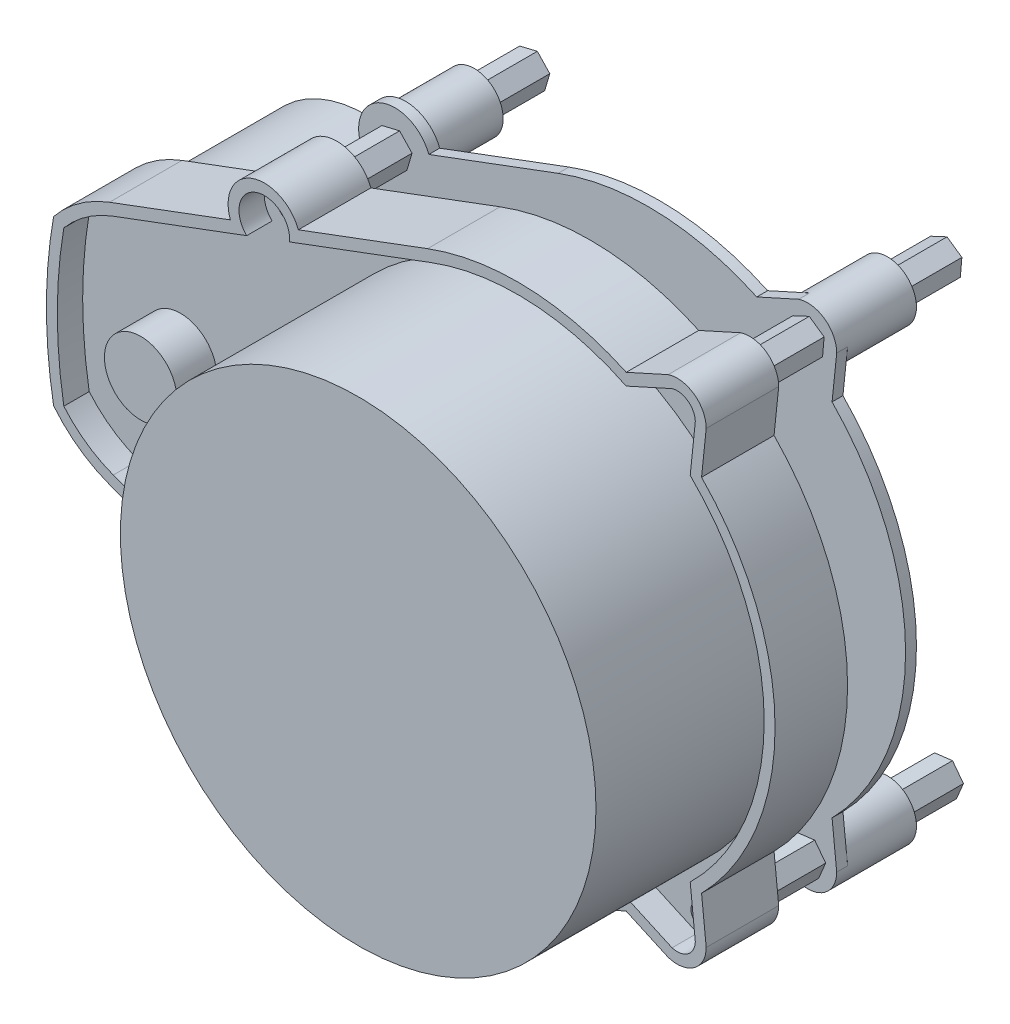
SolidWorks part; units mm, degrees
ref_plane "Plan de face" through (0, 0, 0) normal (0, 0, 1) x (1, 0, 0)
ref_plane "Plan de dessus" through (0, 0, 0) normal (0, 1, 0) x (1, 0, 0)
ref_plane "Plan de droite" through (0, 0, 0) normal (1, 0, 0) x (0, 0, -1)
sketch "Esquisse1" plane through (0, 0, 0) normal (0, 0, 1) x (1, 0, 0)
  line L0 (-12.425, 33.2546) -> (-30.2572, 26.5919)
  line L1 (-56.3, 16.8615) -> (-56.3, -16.8615) construction
  line L2 (-50, 0) -> (0, 0) construction
  line L3 (-12.425, 33.2546) -> (-12.425, -33.2546) construction
  line L5 (-35, 25) -> (-34.9409, 24.8419) construction
  line L6 (-39.6247, 23.0919) -> (-56.3, 16.8615)
  line L7 (-33.4505, 25.3988) -> (-36.4314, 24.2851)
  line L8 (20.756, 34.8016) -> (14.974, 32.1874)
  line L9 (26, 31) -> (25.36, 24.8419)
  line L10 (-65, 0) -> (35.5, 0) construction
  line L11 (55, 0) -> (-55, 0) construction
  line L12 (-35, -25) -> (-34.9409, -24.8419) construction
  line L13 (26, -31) -> (25.36, -24.8419)
  line L14 (20.756, -34.8016) -> (14.974, -32.1874)
  line L15 (-33.4505, -25.3988) -> (-36.4314, -24.2851)
  line L16 (-39.6247, -23.0919) -> (-56.3, -16.8615)
  line L17 (-12.425, -33.2546) -> (-30.2572, -26.5919)
  arc A1 (25.36, -24.8419) -> (25.36, 24.8419) centre (0, 0) ccw
  arc A3 (-64.01, 11.3013) -> (-64.01, -11.3013) centre (0, 0) ccw
  arc A4 (-56.3, 16.8615) -> (-64.01, 11.3013) centre (-50, 0) ccw
  circle A5 centre (22, 31) radius 1.6
  circle A6 centre (-35, 25) radius 1.6
  arc A7 (-30.2572, 26.5919) -> (-39.6247, 23.0919) centre (-34.9409, 24.8419) ccw
  arc A8 (26, 31) -> (20.756, 34.8016) centre (22, 31) ccw
  arc A9 (14.974, 32.1874) -> (-12.425, 33.2546) centre (0, 0) ccw
  arc A10 (14.974, -32.1874) -> (-12.425, -33.2546) centre (0, 0) cw
  arc A11 (26, -31) -> (20.756, -34.8016) centre (22, -31) cw
  arc A12 (-30.2572, -26.5919) -> (-39.6247, -23.0919) centre (-34.9409, -24.8419) cw
  circle A13 centre (-35, -25) radius 1.6
  circle A14 centre (22, -31) radius 1.6
  arc A15 (-56.3, -16.8615) -> (-64.01, -11.3013) centre (-50, 0) cw
  point P28 (-12.425, 0)
  point P29 (-56.3, 0)
  dimension "D1" = 71
  dimension "D4" = 130
  dimension "D6" = 3.2
  dimension "D10" = 10
  dimension "D11" = 8
  dimension "D3" = 50
  dimension "D5" = 31
  dimension "D7" = 22
  dimension "D8" = 35
  dimension "D9" = 25
extrude "Boss.-Extru.1" add sketch "Esquisse1" along normal blind 10 contours A15 L16 A12 L17 A10 L14 A11 L13 A1 L9 A8 L8 A9 L0 A7 L6 A4 A3 A13 A5 A6 A14
sketch "Esquisse2" plane through (0, 0, 10) normal (0, 0, 1) x (1, 0, 0)
  circle A0 centre (0, 0) radius 32.8
  dimension "D1" = 65.6
extrude "Boss.-Extru.2" add sketch "Esquisse2" along normal blind 22
sketch "Esquisse3" plane through (0, 0, 10) normal (0, 0, 1) x (1, 0, 0)
  line L16 (-55.775, -15.4564) -> (-37.3782, -22.33)
  line L17 (14.9568, -30.5335) -> (21.2911, -33.3974)
  line L18 (24.4991, -31.0687) -> (23.7942, -24.2866)
  line L19 (23.7942, 24.2866) -> (24.4991, 31.0687)
  line L20 (21.2911, 33.3974) -> (14.9568, 30.5335)
  line L21 (-11.9, 31.8495) -> (-31.4537, 24.5436)
  line L22 (-55.775, -15.4564) -> (-37.3782, -22.33)
  line L23 (14.9568, -30.5335) -> (21.2911, -33.3974)
  line L24 (24.4991, -31.0687) -> (23.7942, -24.2866)
  line L25 (23.7942, 24.2866) -> (24.4991, 31.0687)
  line L26 (21.2911, 33.3974) -> (14.9568, 30.5335)
  line L27 (-11.9, 31.8495) -> (-31.4537, 24.5436)
  line L28 (-31.4537, -24.5436) -> (-11.9, -31.8495)
  line L29 (-31.4537, -24.5436) -> (-11.9, -31.8495)
  line L30 (-37.3782, 22.33) -> (-55.775, 15.4564)
  line L31 (-37.3782, 22.33) -> (-55.775, 15.4564)
  arc A20 (-62.6, -10.6532) -> (-55.775, -15.4564) centre (-50, 0) ccw
  arc A21 (-11.9, -31.8495) -> (14.9568, -30.5335) centre (0, 0) ccw
  arc A22 (23.7942, -24.2866) -> (23.7942, 24.2866) centre (0, 0) ccw
  arc A23 (14.9568, 30.5335) -> (-11.9, 31.8495) centre (0, 0) ccw
  arc A24 (-55.775, 15.4564) -> (-62.6, 10.6532) centre (-50, 0) ccw
  arc A25 (-62.6, 10.6532) -> (-62.6, -10.6532) centre (0, 0) ccw
  arc A26 (-62.6, -10.6532) -> (-55.775, -15.4564) centre (-50, 0) ccw
  arc A27 (-11.9, -31.8495) -> (14.9568, -30.5335) centre (0, 0) ccw
  arc A28 (23.7942, -24.2866) -> (23.7942, 24.2866) centre (0, 0) ccw
  arc A29 (14.9568, 30.5335) -> (-11.9, 31.8495) centre (0, 0) ccw
  arc A30 (-55.775, 15.4564) -> (-62.6, 10.6532) centre (-50, 0) ccw
  arc A31 (-62.6, 10.6532) -> (-62.6, -10.6532) centre (0, 0) ccw
  arc A32 (-37.3782, -22.33) -> (-31.4537, -24.5436) centre (-34.9409, -24.8419) ccw
  arc A33 (-37.3782, -22.33) -> (-31.4537, -24.5436) centre (-34.9409, -24.8419) ccw
  arc A34 (21.2911, -33.3974) -> (24.4991, -31.0687) centre (22, -31) ccw
  arc A35 (21.2911, -33.3974) -> (24.4991, -31.0687) centre (22, -31) ccw
  arc A36 (24.4991, 31.0687) -> (21.2911, 33.3974) centre (22, 31) ccw
  arc A37 (24.4991, 31.0687) -> (21.2911, 33.3974) centre (22, 31) ccw
  arc A38 (-31.4537, 24.5436) -> (-37.3782, 22.33) centre (-34.9409, 24.8419) ccw
  arc A39 (-31.4537, 24.5436) -> (-37.3782, 22.33) centre (-34.9409, 24.8419) ccw
  dimension "D1" = 1.5
extrude "Enlèv. mat.-Extru.1" cut sketch "Esquisse3" against normal blind 3.5
sketch "Esquisse4" plane through (0, 0, 10) normal (0, 0, -1) x (-1, 0, 0)
  circle A1 centre (0, 0) radius 32.8
  circle A2 centre (0, 0) radius 32.8
  dimension "D1" = 0
extrude "Boss.-Extru.3" add sketch "Esquisse4" along normal up to next
sketch "Esquisse5" plane through (0, 0, 0) normal (0, 0, -1) x (-1, 0, 0)
  circle A0 centre (50, 0) radius 16
  dimension "D2" = 32
  dimension "D1" = 50
extrude "Boss.-Extru.4" add sketch "Esquisse5" along normal blind 19
sketch "Esquisse6" plane through (0, 0, 0) normal (0, 0, -1) x (-1, 0, 0)
  line L1 (-20.4892, -29.0081) -> (-22.9696, -28.6957)
  line L2 (-22.9696, -28.6957) -> (-24.4804, -30.6876)
  line L3 (-24.4804, -30.6876) -> (-23.5108, -32.9919)
  line L4 (-23.5108, -32.9919) -> (-21.0304, -33.3043)
  line L5 (-21.0304, -33.3043) -> (-19.5196, -31.3124)
  line L6 (-19.5196, -31.3124) -> (-20.4892, -29.0081)
  line L7 (36.0868, -22.7486) -> (33.5937, -22.9331)
  line L8 (33.5937, -22.9331) -> (32.5068, -25.1845)
  line L9 (32.5068, -25.1845) -> (33.9132, -27.2514)
  line L10 (33.9132, -27.2514) -> (36.4063, -27.0669)
  line L11 (36.4063, -27.0669) -> (37.4932, -24.8155)
  line L12 (37.4932, -24.8155) -> (36.0868, -22.7486)
  line L13 (36.7203, 26.814) -> (34.2892, 27.3968)
  line L14 (34.2892, 27.3968) -> (32.5689, 25.5828)
  line L15 (32.5689, 25.5828) -> (33.2797, 23.186)
  line L16 (33.2797, 23.186) -> (35.7108, 22.6032)
  line L17 (35.7108, 22.6032) -> (37.4311, 24.4172)
  line L18 (37.4311, 24.4172) -> (36.7203, 26.814)
  line L19 (-19.9522, 32.434) -> (-22.218, 33.4905)
  line L20 (-22.218, 33.4905) -> (-24.2658, 32.0565)
  line L21 (-24.2658, 32.0565) -> (-24.0478, 29.566)
  line L22 (-24.0478, 29.566) -> (-21.782, 28.5095)
  line L23 (-21.782, 28.5095) -> (-19.7342, 29.9435)
  line L24 (-19.7342, 29.9435) -> (-19.9522, 32.434)
  circle A0 centre (-22, -31) radius 2.1651 construction
  circle A1 centre (35, -25) radius 2.1651 construction
  circle A2 centre (35, 25) radius 2.1651 construction
  circle A3 centre (-22, 31) radius 2.1651 construction
  circle A4 centre (35, -25) radius 1
  circle A5 centre (35, 25) radius 1
  circle A6 centre (-22, 31) radius 1
  circle A7 centre (-22, -31) radius 1
  dimension "D2" = 2
  dimension "D1" = 5
extrude "Boss.-Extru.5" add sketch "Esquisse6" along normal blind 27
ref_plane "Plan1" through (0, 0, -8) normal (0, 0, -1) x (-1, 0, 0)
sketch "Esquisse7" plane through (0, 0, -8) normal (0, 0, -1) x (-1, 0, 0)
  line L0 (50, 0) -> (80, 0) construction
  line L8 (56.3, 16.8615) -> (39.6247, 23.0919)
  line L9 (30.2572, 26.5919) -> (12.425, 33.2546)
  line L10 (-14.974, 32.1874) -> (-20.756, 34.8016)
  line L11 (-26, 31) -> (-25.36, 24.8419)
  line L12 (-25.36, -24.8419) -> (-26, -31)
  line L13 (-20.756, -34.8016) -> (-14.974, -32.1874)
  line L14 (12.425, -33.2546) -> (30.2572, -26.5919)
  line L15 (39.6247, -23.0919) -> (56.3, -16.8615)
  line L17 (30.2572, 26.5919) -> (12.425, 33.2546)
  line L18 (-14.974, 32.1874) -> (-20.756, 34.8016)
  line L19 (-26, 31) -> (-25.36, 24.8419)
  line L20 (-25.36, -24.8419) -> (-26, -31)
  line L21 (-20.756, -34.8016) -> (-14.974, -32.1874)
  line L22 (12.425, -33.2546) -> (30.2572, -26.5919)
  arc A0 (39.6247, 23.0919) -> (39.6247, -23.0919) centre (80, 0) ccw
  arc A12 (64.69, 6.3407) -> (64.69, -6.3407) centre (50, 0) ccw
  arc A13 (64.69, 6.3407) -> (64.01, 11.3013) centre (0, 0) ccw
  arc A14 (64.01, 11.3013) -> (56.3, 16.8615) centre (50, 0) ccw
  arc A15 (39.6247, 23.0919) -> (30.2572, 26.5919) centre (34.9409, 24.8419) ccw
  arc A16 (12.425, 33.2546) -> (-14.974, 32.1874) centre (0, 0) ccw
  arc A17 (-20.756, 34.8016) -> (-26, 31) centre (-22, 31) ccw
  arc A18 (-25.36, 24.8419) -> (-25.36, -24.8419) centre (0, 0) ccw
  arc A19 (-26, -31) -> (-20.756, -34.8016) centre (-22, -31) ccw
  arc A20 (-14.974, -32.1874) -> (12.425, -33.2546) centre (0, 0) ccw
  arc A21 (30.2572, -26.5919) -> (39.6247, -23.0919) centre (34.9409, -24.8419) ccw
  arc A22 (56.3, -16.8615) -> (64.01, -11.3013) centre (50, 0) ccw
  arc A23 (64.01, -11.3013) -> (64.69, -6.3407) centre (0, 0) ccw
  arc A27 (39.6247, 23.0919) -> (30.2572, 26.5919) centre (34.9409, 24.8419) ccw
  arc A28 (12.425, 33.2546) -> (-14.974, 32.1874) centre (0, 0) ccw
  arc A29 (-20.756, 34.8016) -> (-26, 31) centre (-22, 31) ccw
  arc A30 (-25.36, 24.8419) -> (-25.36, -24.8419) centre (0, 0) ccw
  arc A31 (-26, -31) -> (-20.756, -34.8016) centre (-22, -31) ccw
  arc A32 (-14.974, -32.1874) -> (12.425, -33.2546) centre (0, 0) ccw
  arc A33 (30.2572, -26.5919) -> (39.6247, -23.0919) centre (34.9409, -24.8419) ccw
  dimension "D2" = 30
  dimension "D1" = 0
extrude "Boss.-Extru.6" add sketch "Esquisse7" along normal blind 1.5
sketch "Esquisse8" plane through (0, 0, 6.5) normal (0, 0, 1) x (1, 0, 0)
  circle A0 centre (-50, 0) radius 5
  dimension "D1" = 10
extrude "Boss.-Extru.7" add sketch "Esquisse8" along normal blind 5.5
sketch "Sketch2" plane through (0, 0, -9.5) normal (0, 0, -1) x (-1, 0, 0)
  circle A0 centre (-22, 31) radius 3
  circle A1 centre (35, 25) radius 3
  circle A2 centre (-22, -31) radius 3
  circle A3 centre (35, -25) radius 3
  circle A4 centre (-22, 31) radius 4
  circle A5 centre (35, 25) radius 4
  circle A6 centre (-22, -31) radius 4
  circle A7 centre (35, -25) radius 4
  point P0 (0, 0)
  dimension "D1" = 6
  dimension "D2" = 1
extrude "Boss-Extrude1" add sketch "Sketch2" along normal blind 9.5
